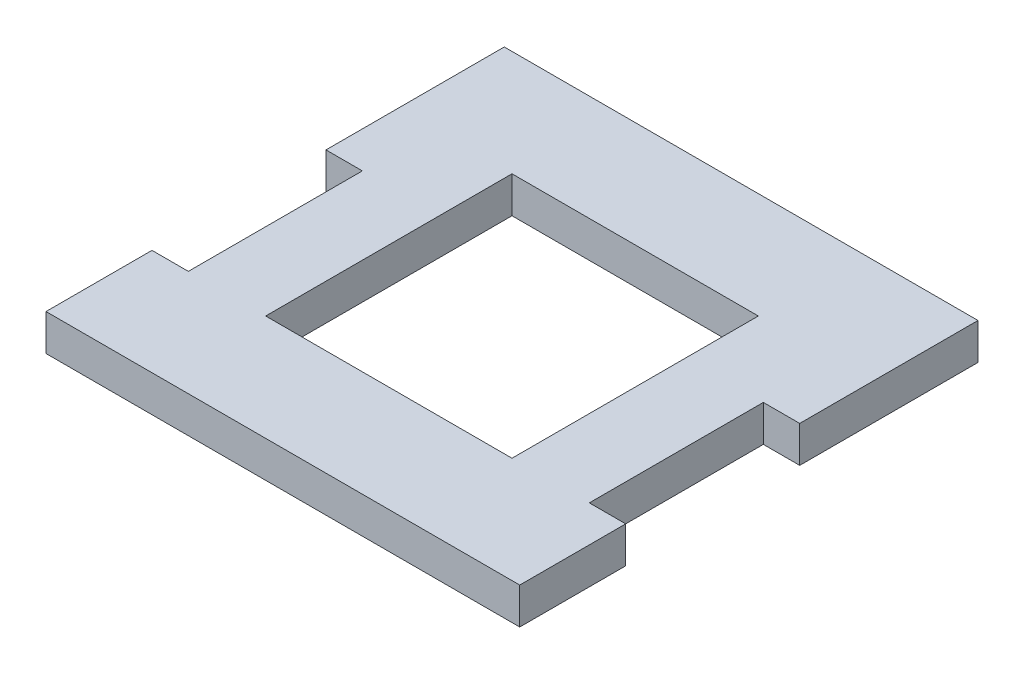
SolidWorks part; units mm, degrees
ref_plane "Front Plane" through (0, 0, 0) normal (0, 0, 1) x (1, 0, 0)
ref_plane "Top Plane" through (0, 0, 0) normal (0, 1, 0) x (1, 0, 0)
ref_plane "Right Plane" through (0, 0, 0) normal (1, 0, 0) x (0, 0, -1)
sketch "Sketch1" plane through (0, 0, 0) normal (0, 1, 0) x (1, 0, 0)
  line L1 (0, 0) -> (41.35, 0)
  line L2 (0, 0) -> (0, 40)
  line L3 (0, 40) -> (41.35, 40)
  line L4 (41.35, 0) -> (41.35, 40)
  line L5 (9.925, 9.25) -> (31.425, 9.25)
  line L6 (9.925, 9.25) -> (9.925, 30.75)
  line L7 (9.925, 30.75) -> (31.425, 30.75)
  line L8 (31.425, 9.25) -> (31.425, 30.75)
  point P9 (20.675, 9.25)
  point P10 (20.675, 0)
  point P11 (9.925, 20)
  point P12 (0, 20)
  dimension "D1" = 41.35
  dimension "D2" = 40
  dimension "D3" = 21.5
  dimension "D4" = 21.5
extrude "Boss-Extrude1" add sketch "Sketch1" along normal blind 3.175 contours L5 L8 L7 L6
sketch "Sketch2" plane through (0, 3.175, 0) normal (0, 1, 0) x (1, 0, 0)
  line L0 (41.35, 0) -> (41.35, 40) construction
  line L1 (38.175, 24.438) -> (41.35, 24.438)
  line L2 (38.175, 24.438) -> (38.175, 9.25)
  line L3 (38.175, 9.25) -> (41.35, 9.25)
  line L4 (41.35, 24.438) -> (41.35, 9.25)
  line L5 (9.925, 9.25) -> (31.425, 9.25) construction
  line L6 (0, 40) -> (0, 0) construction
  line L7 (3.175, 24.438) -> (0, 24.438)
  line L8 (3.175, 24.438) -> (3.175, 9.25)
  line L9 (3.175, 9.25) -> (0, 9.25)
  line L10 (0, 24.438) -> (0, 9.25)
  line L11 (41.35, 40) -> (0, 40) construction
  point P16 (0, 0)
  point P17 (0, 0)
  dimension "D1" = 3.175
  dimension "D2" = 15.562
extrude "Cut-Extrude1" cut sketch "Sketch2" against normal through all
